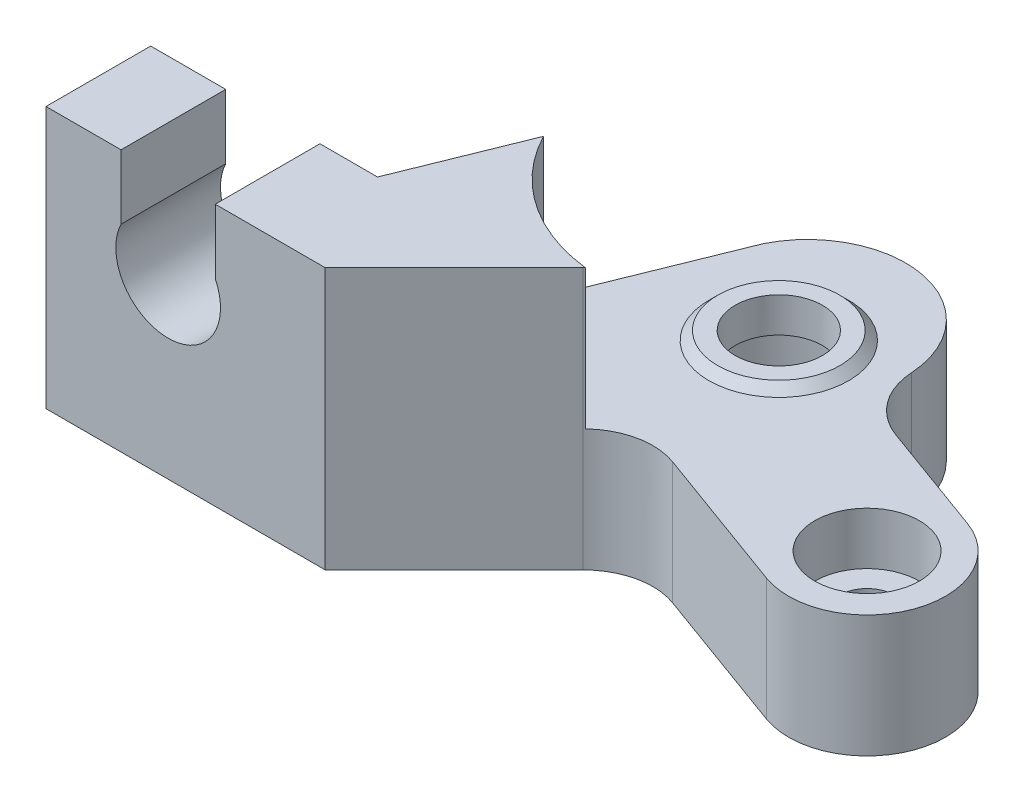
SolidWorks part; units mm, degrees
ref_plane "Front Plane" through (0, 0, 0) normal (0, 0, 1) x (1, 0, 0)
ref_plane "Top Plane" through (0, 0, 0) normal (0, 1, 0) x (1, 0, 0)
ref_plane "Right Plane" through (0, 0, 0) normal (1, 0, 0) x (0, 0, -1)
sketch "Sketch1" plane through (0, 0, 0) normal (0, 1, 0) x (1, 0, 0)
  line L0 (0, 0) -> (16, 0)
  line L1 (16, 0) -> (23.3905, 7.3905)
  line L2 (27.587, 8.3208) -> (36.0442, 5.2426)
  line L3 (39.1224, 13.6999) -> (32.6385, 16.0598)
  line L4 (0, 0) -> (0, 6)
  line L5 (0, 6) -> (13, 6)
  line L6 (13, 6) -> (19.3683, 21.7621)
  arc A0 (36.0442, 5.2426) -> (39.1224, 13.6999) centre (37.5833, 9.4713) ccw
  arc A1 (27.587, 8.3208) -> (23.3905, 7.3905) centre (26.2189, 4.5621) ccw
  arc A2 (30.0137, 19.5802) -> (19.3683, 21.7621) centre (24.3987, 19.245) ccw
  arc A3 (30.0137, 19.5802) -> (32.6385, 16.0598) centre (34.0066, 19.8186) ccw
  point P9 (25.1924, 9.1924)
  point P15 (23.9073, 17.1094)
  point P19 (23.7738, 16.9829)
  dimension "D5" = 4
  dimension "D7" = 4.5
  dimension "D8" = 8
  dimension "D10" = 11.25
  dimension "D15" = 13
  dimension "D1" = 16
  dimension "D2" = 135
  dimension "D3" = 13
  dimension "D4" = 65
  dimension "D6" = 9
  dimension "D9" = 6.9
  dimension "D11" = 6
  dimension "D12" = 13
  dimension "D13" = 112
  dimension "D14" = 17
extrude "Boss-Extrude2" add sketch "Sketch1" along normal blind 15 contours L6 A2 A3 L3 A0 L2 A1 L1 L0 L4 L5
sketch "Sketch4" plane through (0, 15, 0) normal (0, 1, 0) x (1, 0, 0)
  line L1 (13, 6) -> (19.3683, 21.7621) construction
  line L4 (39.1224, 13.6999) -> (32.6385, 16.0598) construction
  line L5 (27.5271, 7.8203) -> (39.5633, 1.8379)
  line L7 (39.5633, 1.8379) -> (45.0396, 12.8559)
  line L8 (34.5884, 18.0504) -> (45.0396, 12.8559)
  arc A0 (34.5884, 18.0504) -> (27.5271, 7.8203) centre (24.6105, 17.3855) ccw
  dimension "D1" = 20
  dimension "D2" = 1.5
  dimension "D3" = 6.5
extrude "Cut-Extrude2" cut sketch "Sketch4" against normal blind 8
sketch "Sketch5" plane through (0, 7, 0) normal (0, 1, 0) x (1, 0, 0)
  circle A0 centre (24.6105, 17.3855) radius 4
  dimension "D1" = 8
extrude "Boss-Extrude3" add sketch "Sketch5" along normal blind 0.5 draft 45
sketch "Sketch6" plane through (0, 7.5, 0) normal (0, 1, 0) x (1, 0, 0)
  circle A0 centre (24.6105, 17.3855) radius 2.5
  dimension "D1" = 5
extrude "Cut-Extrude3" cut sketch "Sketch6" against normal blind 2
sketch "Sketch7" plane through (0, 0, 0) normal (0, -1, 0) x (1, 0, 0)
  circle A0 centre (24.6105, -17.3855) radius 4.5
  dimension "D1" = 9
extrude "Cut-Extrude4" cut sketch "Sketch7" against normal blind 5.5
sketch "Sketch8" plane through (0, 0, 0) normal (0, 0, 1) x (1, 0, 0)
  line L0 (0, 0) -> (16, 0) construction
  line L1 (0, 15) -> (0, 0) construction
  line L2 (4.3, 11.3077) -> (4.3, 15)
  line L3 (0, 15) -> (16, 15) construction
  line L4 (7, 13) -> (7, 16.3995) construction
  line L5 (9.7, 11.3077) -> (9.7, 15)
  line L6 (9.7, 15) -> (4.3, 15)
  arc A0 (4.3, 11.3077) -> (9.7, 11.3077) centre (7, 10) ccw
  dimension "D1" = 6
  dimension "D2" = 10
  dimension "D3" = 7
  dimension "D4" = 4.3
extrude "Cut-Extrude5" cut sketch "Sketch8" against normal blind 15
sketch "Sketch9" plane through (0, 7, 0) normal (0, 1, 0) x (1, 0, 0)
  circle A0 centre (37.5833, 9.4713) radius 3
  dimension "D1" = 6
extrude "Cut-Extrude6" cut sketch "Sketch9" against normal blind 3
sketch "Sketch10" plane through (0, 4, 0) normal (0, 1, 0) x (1, 0, 0)
  circle A0 centre (37.5833, 9.4713) radius 1.6
  dimension "D1" = 3.2
extrude "Cut-Extrude7" cut sketch "Sketch10" against normal blind 4
